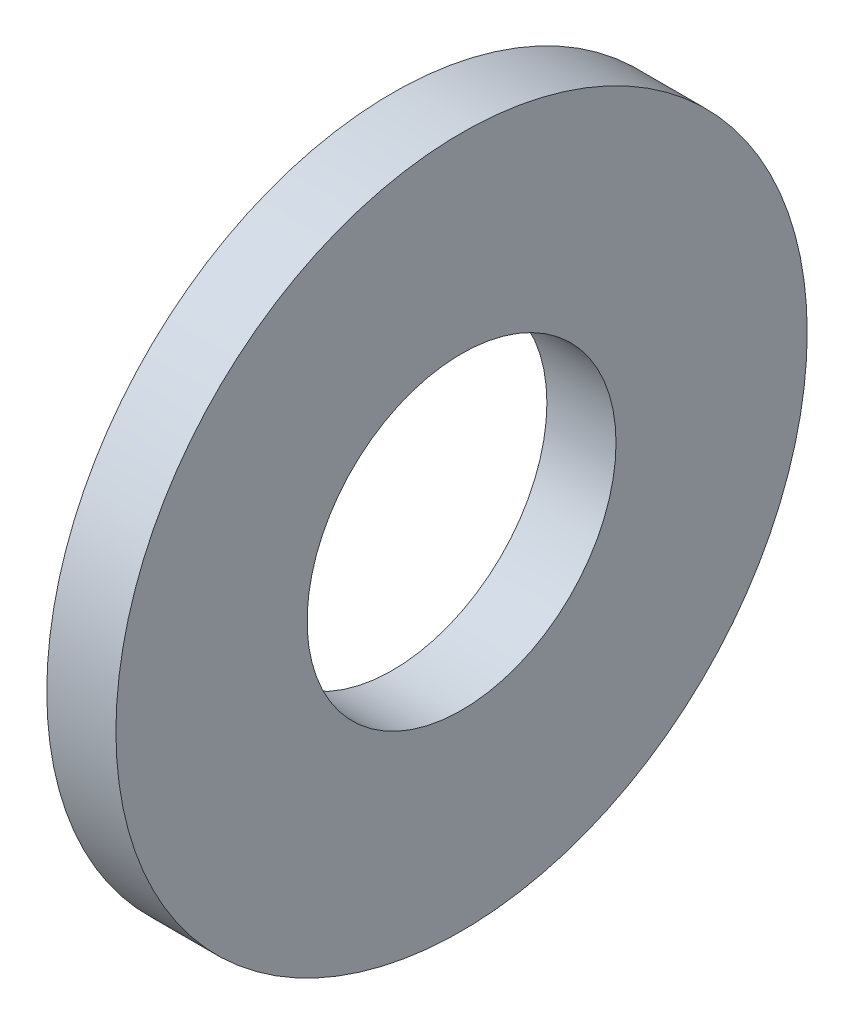
SolidWorks part; units mm, degrees
ref_plane "Plane1" through (0, 0, 0) normal (0, 0, 1) x (1, 0, 0)
ref_plane "Plane2" through (0, 0, 0) normal (0, 1, 0) x (1, 0, 0)
ref_plane "Plane3" through (0, 0, 0) normal (1, 0, 0) x (0, 0, -1)
sketch "Sketch1" plane through (0, 0, 0) normal (1, 0, 0) x (0, 0, -1)
  circle A0 centre (0, 0) radius 3.575
  circle A1 centre (0, 0) radius 8
  dimension "Insid_dia" = 7.15
  dimension "OutsideDia" = 16
extrude "Base-Extrude" add sketch "Sketch1" along normal blind 1.6
